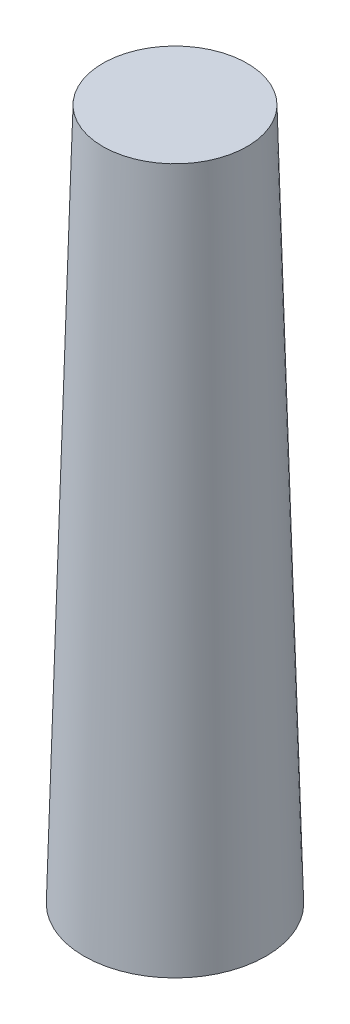
SolidWorks part; units mm, degrees
ref_plane "Přední rovina" through (0, 0, 0) normal (0, 0, 1) x (1, 0, 0)
ref_plane "Horní rovina" through (0, 0, 0) normal (0, 1, 0) x (1, 0, 0)
ref_plane "Pravá rovina" through (0, 0, 0) normal (1, 0, 0) x (0, 0, -1)
sketch "Skica1" plane through (0, 0, 0) normal (0, 0, 1) x (1, 0, 0)
  line L0 (-17.7564, 0) -> (22.8893, 0) construction
  line L1 (-5.5, 0) -> (-4, 55)
  line L2 (-4, 55) -> (0, 55)
  line L3 (0, 59.3444) -> (0, -6.1713) construction
  line L4 (0, 55) -> (0, 57)
  line L5 (0, 57) -> (-5.9455, 57)
  line L6 (-5.9455, 57) -> (-7.5, 0)
  line L7 (-7.5, 0) -> (-5.5, 0)
  dimension "D1" = 5.5
  dimension "D2" = 4
  dimension "D3" = 55
  dimension "D4" = 2
  dimension "D5" = 2
revolve "Rotovat1" add sketch "Skica1" angle 360 about L3
